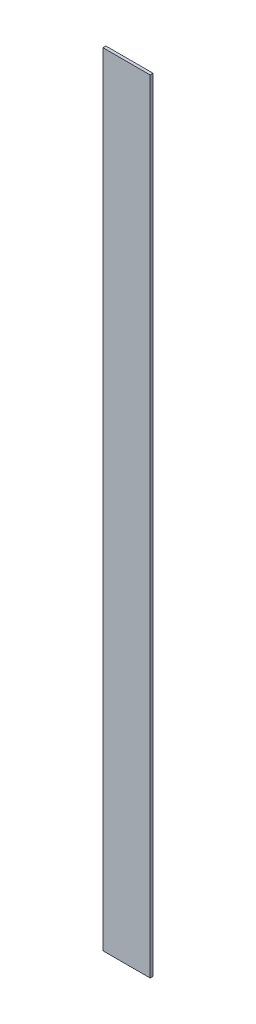
SolidWorks part; units mm, degrees
ref_plane "Front" through (0, 0, 0) normal (0, 0, 1) x (1, 0, 0)
ref_plane "Top" through (0, 0, 0) normal (0, 1, 0) x (1, 0, 0)
ref_plane "Right" through (0, 0, 0) normal (1, 0, 0) x (0, 0, -1)
sketch "Sketch1" plane through (0, 0, 0) normal (0, 0, 1) x (1, 0, 0)
  line L1 (-32.3769, 25.1171) -> (18.4231, 25.1171)
  line L2 (-32.3769, 25.1171) -> (-32.3769, -817.9089)
  line L3 (-32.3769, -817.9089) -> (18.4231, -817.9089)
  line L4 (18.4231, 25.1171) -> (18.4231, -817.9089)
  dimension "D1" = 50.8
  dimension "D2" = 843.026
extrude "Boss-Extrude1" add sketch "Sketch1" along normal blind 3.175
